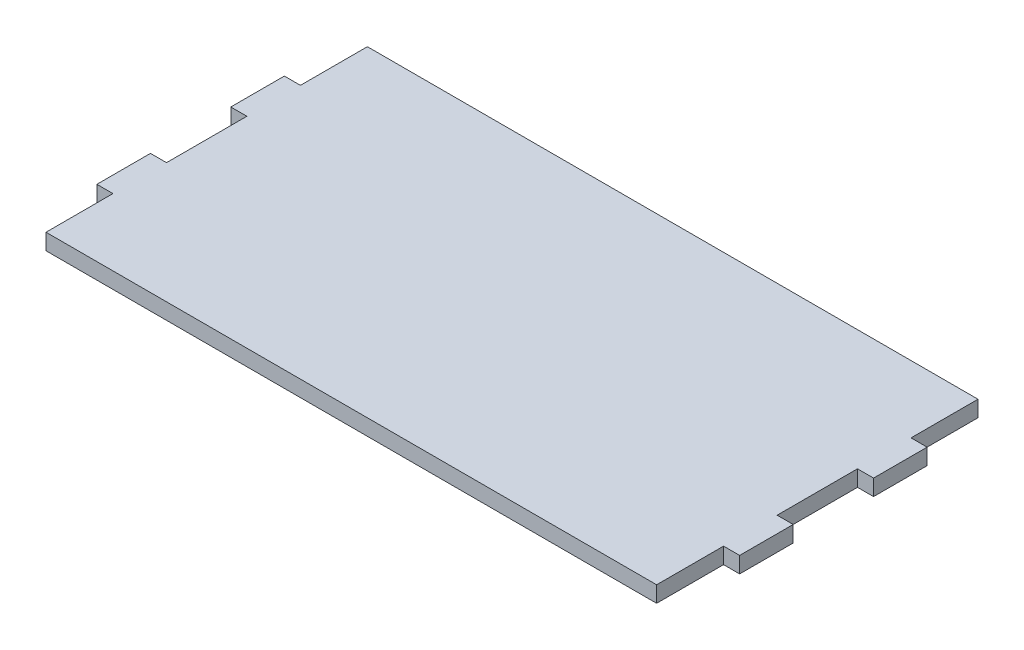
SolidWorks part; units mm, degrees
ref_plane "Alzado" through (0, 0, 0) normal (0, 0, 1) x (1, 0, 0)
ref_plane "Planta" through (0, 0, 0) normal (0, 1, 0) x (1, 0, 0)
ref_plane "Vista lateral" through (0, 0, 0) normal (1, 0, 0) x (0, 0, -1)
sketch "Croquis1" plane through (0, 0, 0) normal (0, 1, 0) x (1, 0, 0)
  line L0 (-57, 17.5) -> (-60, 17.5)
  line L1 (57, 30) -> (-57, 30)
  line L2 (57, 30) -> (57, 17.5)
  line L3 (57, -30) -> (-57, -30)
  line L4 (-57, 30) -> (-57, 17.5)
  line L5 (57, 30) -> (-57, -30) construction
  line L6 (57, -30) -> (-57, 30) construction
  line L7 (-60, 17.5) -> (-60, 7.5)
  line L8 (-60, 7.5) -> (-57, 7.5)
  line L9 (-57, -7.5) -> (-60, -7.5)
  line L10 (-60, -7.5) -> (-60, -17.5)
  line L11 (-60, -17.5) -> (-57, -17.5)
  line L12 (0, 0) -> (-82.9047, 0) construction
  line L13 (0, 0) -> (0, -54.3177) construction
  line L14 (60, -17.5) -> (57, -17.5)
  line L15 (60, -7.5) -> (60, -17.5)
  line L16 (57, -7.5) -> (60, -7.5)
  line L17 (60, 7.5) -> (57, 7.5)
  line L18 (60, 17.5) -> (60, 7.5)
  line L19 (57, 17.5) -> (60, 17.5)
  line L20 (-57, 7.5) -> (-57, -7.5)
  line L21 (-57, -17.5) -> (-57, -30)
  line L22 (57, -17.5) -> (57, -30)
  line L23 (57, 7.5) -> (57, -7.5)
  point P0 (0, 0)
  point P25 (-57, 6.2919)
  point P26 (-58.5, -7.5)
  dimension "D1" = 60
  dimension "D2" = 114
  dimension "D3" = 3
  dimension "D4" = 10
  dimension "D5" = 3
  dimension "D6" = 10
  dimension "D7" = 15
extrude "Saliente-Extruir1" add sketch "Croquis1" along normal blind 3
